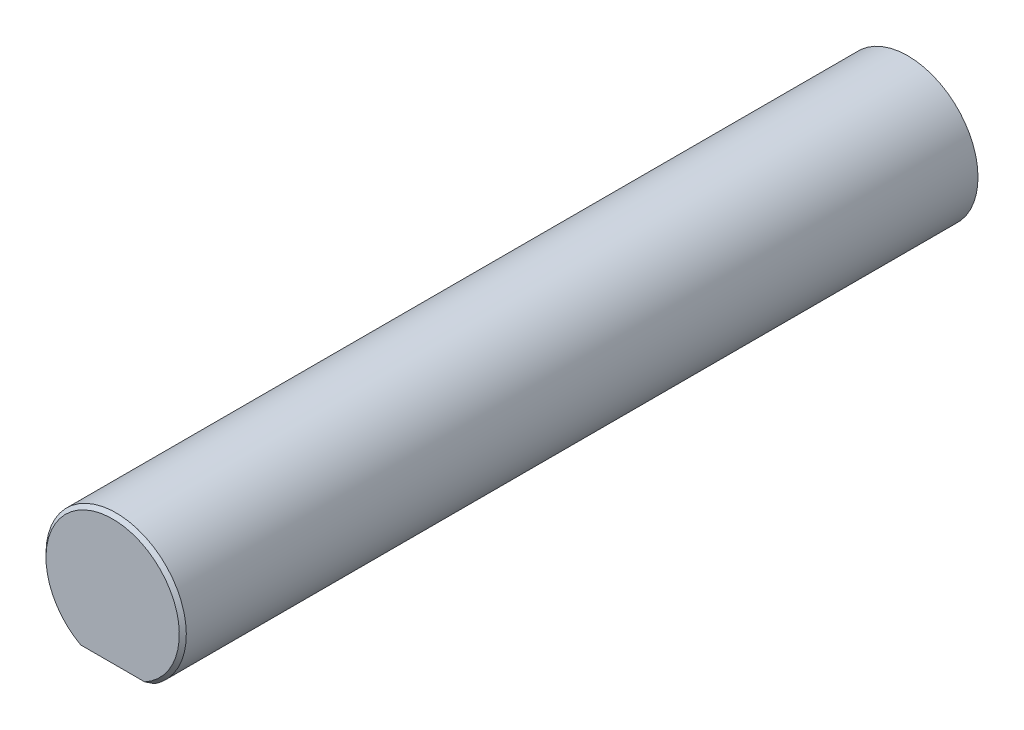
SolidWorks part; units mm, degrees
material "Cast Stainless Steel"
ref_plane "Front Plane" through (0, 0, 0) normal (0, 0, 1) x (1, 0, 0)
ref_plane "Top Plane" through (0, 0, 0) normal (0, 1, 0) x (1, 0, 0)
ref_plane "Right Plane" through (0, 0, 0) normal (1, 0, 0) x (0, 0, -1)
sketch "Sketch1" plane through (0, 0, 0) normal (0, 0, 1) x (1, 0, 0)
  circle A0 centre (0, 0) radius 3
  dimension "D1" = 6
extrude "Boss-Extrude1" add sketch "Sketch1" along normal blind 22 contours A0
sketch "Sketch2" plane through (0, 0, 22) normal (0, 0, 1) x (1, 0, 0)
  line L0 (-1.6583, -2.5) -> (1.6583, -2.5)
  circle A0 centre (0, 0) radius 3 construction
  arc A1 (-1.6583, -2.5) -> (1.6583, -2.5) centre (0, 0) cw
  circle M2 centre (0, 0) radius 3
  dimension "D1" = 2.5
extrude "Boss-Extrude2" add sketch "Sketch2" along normal blind 12 contours L0 M2
chamfer "Chamfer1" distance 0.15 angle 45 1 edges at (0, 3, 34)
